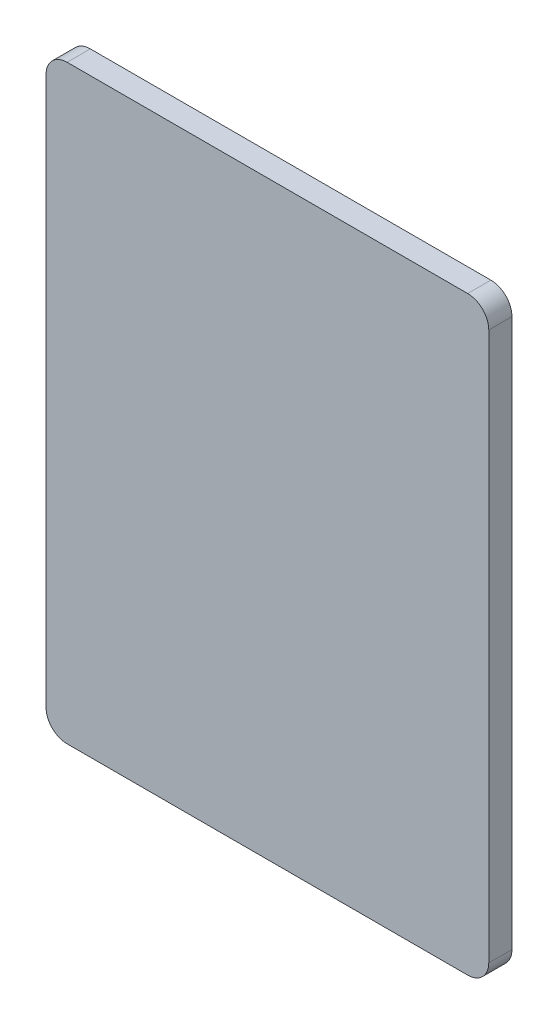
SolidWorks part; units mm, degrees
ref_plane "Front Plane" through (0, 0, 0) normal (0, 0, 1) x (1, 0, 0)
ref_plane "Top Plane" through (0, 0, 0) normal (0, 1, 0) x (1, 0, 0)
ref_plane "Right Plane" through (0, 0, 0) normal (1, 0, 0) x (0, 0, -1)
sketch "Sketch2" plane through (0, 0, 0) normal (0, 0, 1) x (1, 0, 0)
  line L1 (-105, 140) -> (105, 140)
  line L2 (-105, 140) -> (-105, -140)
  line L3 (-105, -140) -> (105, -140)
  line L4 (105, 140) -> (105, -140)
  line L5 (-105, 140) -> (105, -140) construction
  line L6 (-105, -140) -> (105, 140) construction
  point P0 (0, 0)
  dimension "D1" = 210
  dimension "D2" = 280
extrude "Boss-Extrude1" add sketch "Sketch2" along normal blind 11
fillet "Fillet1" radius 10 4 edges at (-105, -140, 5.5) (-105, 140, 5.5) (105, 140, 5.5) (105, -140, 5.5)
